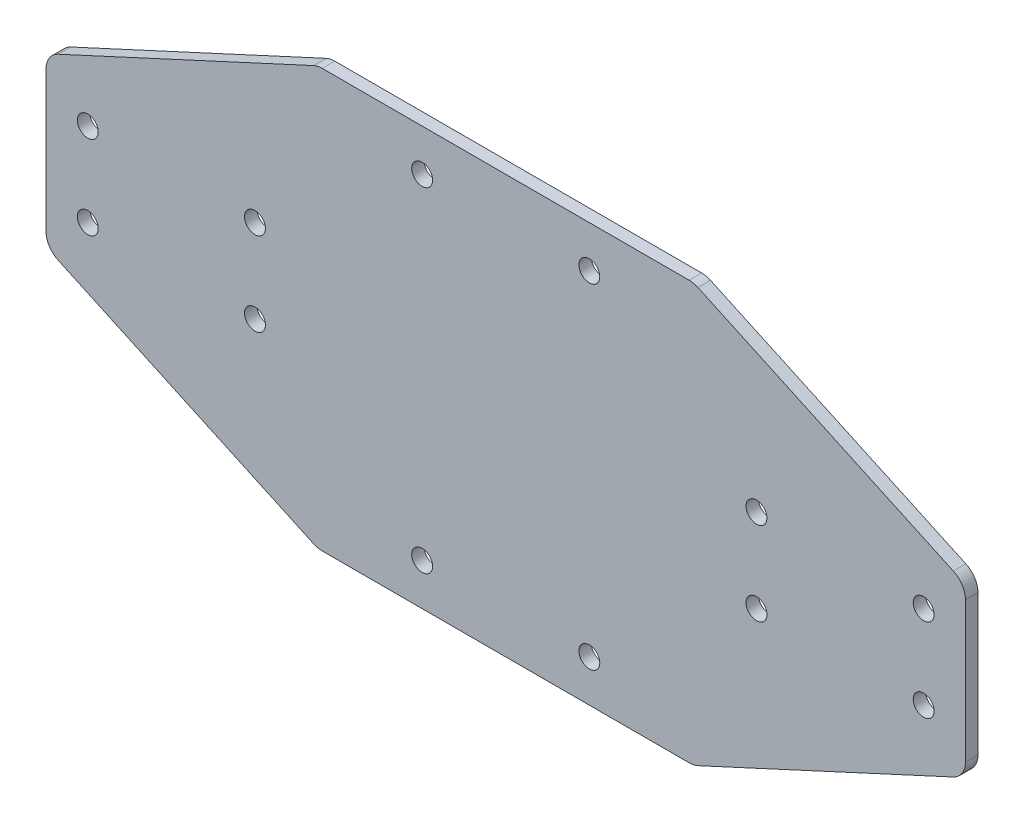
SolidWorks part; units mm, degrees
ref_plane "Front Plane" through (0, 0, 0) normal (0, 0, 1) x (1, 0, 0)
ref_plane "Top Plane" through (0, 0, 0) normal (0, 1, 0) x (1, 0, 0)
ref_plane "Right Plane" through (0, 0, 0) normal (1, 0, 0) x (0, 0, -1)
sketch "Sketch1" plane through (0, 0, 0) normal (0, 0, 1) x (1, 0, 0)
  line L0 (-110, 20) -> (-110, -20)
  line L1 (-110, -20) -> (-45, -50)
  line L2 (-45, -50) -> (45, -50)
  line L3 (45, -50) -> (110, -20)
  line L4 (110, -20) -> (110, 20)
  line L5 (110, 20) -> (45, 50)
  line L6 (45, 50) -> (-45, 50)
  line L7 (-45, 50) -> (-110, 20)
  line L8 (0, 0) -> (245.1765, 0) construction
  line L9 (245.1765, 0) -> (0, 0) construction
  line L10 (0, 0) -> (0, 133.4118) construction
  point P11 (0, 50)
  point P13 (0, -50)
  point P14 (-110, 0)
  point P15 (110, 0)
  dimension "D1" = 40
  dimension "D2" = 90
  dimension "D3" = 220
  dimension "D4" = 100
extrude "Boss-Extrude1" add sketch "Sketch1" along normal blind 3
sketch "Sketch2" plane through (0, 0, 3) normal (0, 0, 1) x (1, 0, 0)
  line L0 (0, 0) -> (110.357, 0) construction
  line L1 (110.357, 0) -> (0, 0) construction
  line L2 (0, 0) -> (0, 67.6487) construction
  circle A0 centre (60, 10) radius 2.5
  dimension "D1" = 5
  dimension "D2" = 10
  dimension "D3" = 60
extrude "Cut-Extrude1" cut sketch "Sketch2" against normal through all
pattern_linear "LPattern1" count 2 spacing 40 along (1, 0, 0) count 2 spacing 20 along (0, -1, 0) of "Cut-Extrude1"
mirror "Mirror1" about plane through (0, 0, 0) normal (1, 0, 0) of "LPattern1", "Cut-Extrude1"
sketch "Sketch3" plane through (0, 0, 3) normal (0, 0, 1) x (1, 0, 0)
  line L0 (0, 0) -> (0, 50) construction
  line L1 (45, 50) -> (-45, 50) construction
  circle A1 centre (20, 40) radius 2.5
  circle A2 centre (-20, 40) radius 2.5
  dimension "D1" = 5
  dimension "D3" = 10
  dimension "D4" = 20
extrude "Cut-Extrude2" cut sketch "Sketch3" against normal through all
mirror "Mirror2" about plane through (0, 0, 0) normal (0, 1, 0) of "Cut-Extrude2"
fillet "Fillet1" radius 5 8 edges at (-45, -50, 1.5) (45, -50, 1.5) (110, -20, 1.5) (110, 20, 1.5) (45, 50, 1.5) (-45, 50, 1.5) (-110, -20, 1.5) (-110, 20, 1.5)
